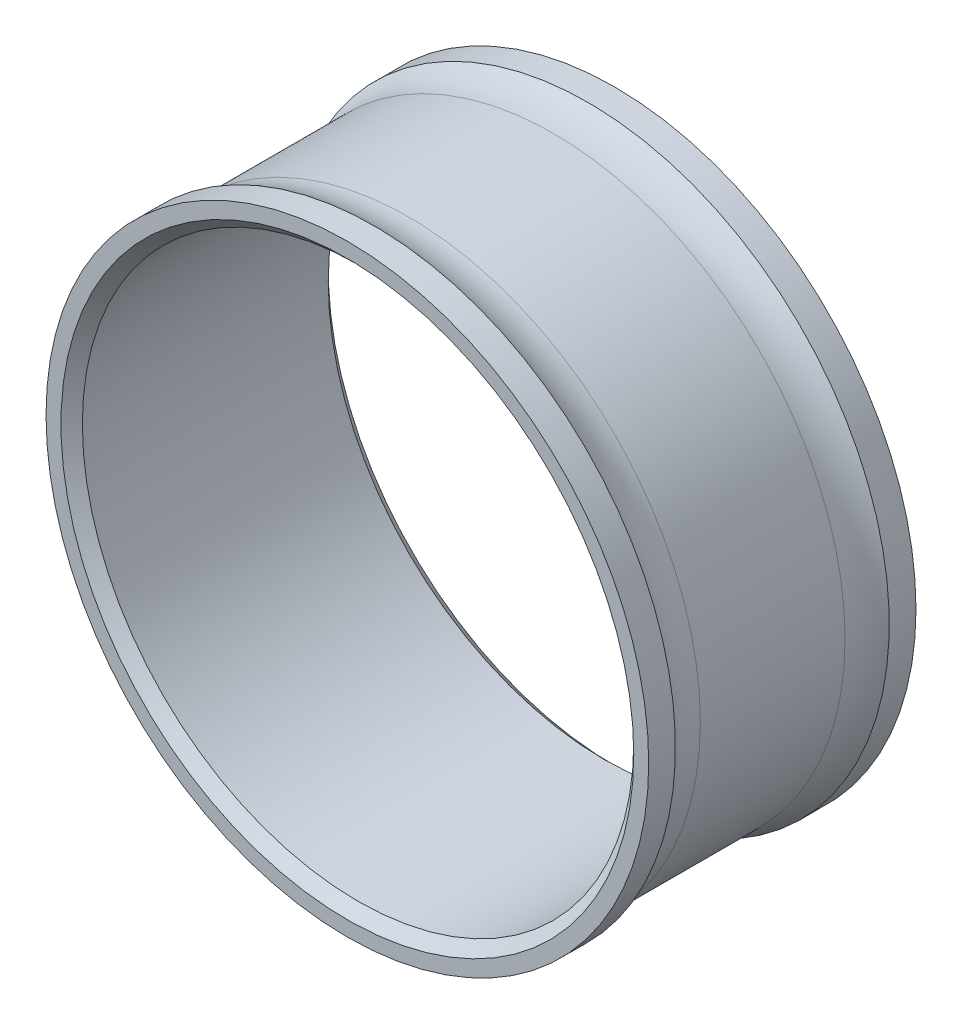
SolidWorks part; units mm, degrees
material "6061-T6 (SS)"
ref_plane "Front Plane" through (0, 0, 0) normal (0, 0, 1) x (1, 0, 0)
ref_plane "Top Plane" through (0, 0, 0) normal (0, 1, 0) x (1, 0, 0)
ref_plane "Right Plane" through (0, 0, 0) normal (1, 0, 0) x (0, 0, -1)
sketch "Sketch1" plane through (0, 0, 0) normal (0, 0, 1) x (1, 0, 0)
  circle A0 centre (0, 0) radius 32.5 construction
  circle A1 centre (0, 0) radius 35.8013
  circle A2 centre (0, 0) radius 32.754
  dimension "D1" = 65
  dimension "D2" = 71.6026
  dimension "D3" = 0.254
extrude "Boss-Extrude1" add sketch "Sketch1" along normal mid plane 31.75
chamfer "Chamfer1" distance 1.27 angle 45 2 edges at (32.754, 0, -15.875) (32.754, 0, 15.875)
sketch "Sketch6" plane through (0, 0, 0) normal (0, 1, 0) x (1, 0, 0)
  line L0 (34.659, -8.5977) -> (34.659, 8.5977)
  line L2 (0, 0) -> (34.659, 0) construction
  line L3 (35.8013, 15.875) -> (-35.8013, 15.875) construction
  line L4 (35.8013, 12.7) -> (35.8013, -12.7)
  line L5 (0, 15.875) -> (0, -15.875) construction
  line L7 (32.754, 14.605) -> (32.754, -15.875) construction
  line L8 (-35.8013, -15.875) -> (35.8013, -15.875) construction
  line L9 (32.754, 14.605) -> (-32.754, 14.605) construction
  line L10 (34.024, 15.875) -> (-34.024, 15.875) construction
  arc A0 (35.8013, 12.7) -> (34.659, 8.5977) centre (42.5965, 8.5977) ccw
  arc A1 (35.8013, -12.7) -> (34.659, -8.5977) centre (42.5965, -8.5977) cw
  point P4 (32.754, 14.605)
  point P9 (35.8013, 15.875)
  point P18 (35.8013, 0)
  dimension "D2" = 7.9375
  dimension "D1" = 1.905
  dimension "D3" = 3.175
revolve "Cut-Revolve2" cut sketch "Sketch6" angle 360 about L5
sketch "Sketch3" plane through (0, 0, 0) normal (0, 1, 0) x (1, 0, 0)
  line L0 (0, 9.525) -> (0, -9.525) construction
  line L1 (3.175, 9.525) -> (3.175, -9.525)
  line L2 (-3.175, 9.525) -> (-3.175, -9.525)
  line L3 (35.8013, 15.875) -> (-35.8013, 15.875) construction
  arc A0 (3.175, 9.525) -> (-3.175, 9.525) centre (0, 9.525) ccw
  arc A1 (-3.175, -9.525) -> (3.175, -9.525) centre (0, -9.525) ccw
  point P3 (0, 0)
  point P8 (0, 12.7)
  dimension "D2" = 3.175
  dimension "D1" = 3.175
extrude "Cut-Extrude1" [suppressed] cut sketch "Sketch3" against normal through all
pattern_circular "CirPattern1" [suppressed] count 19 over 360
sketch "Sketch7" plane through (0, 0, -15.875) normal (0, 0, -1) x (-1, 0, 0)
  circle A0 centre (0, 0) radius 31.75
  circle A1 centre (0, 0) radius 38.1
  dimension "D1" = 63.5
  dimension "D2" = 76.2
sketch "Sketch8" [suppressed] plane through (0, 0, 0) normal (0, 1, 0) x (1, 0, 0)
  line L0 (-2.4644, 9.1974) -> (2.4644, -9.1974) construction
  line L1 (-34.7479, 9.1974) -> (34.7479, 9.1974) construction
  line L2 (-34.7479, -9.1974) -> (34.7479, -9.1974) construction
  line L3 (-5.5312, 8.3756) -> (-0.6024, -10.0191)
  line L4 (0.6024, 10.0191) -> (5.5312, -8.3756)
  line L5 (0, 9.525) -> (0, -9.525) construction
  arc A0 (0.6024, 10.0191) -> (-5.5312, 8.3756) centre (-2.4644, 9.1974) ccw
  arc A1 (-0.6024, -10.0191) -> (5.5312, -8.3756) centre (2.4644, -9.1974) ccw
  arc A2 (3.175, 9.525) -> (-3.175, 9.525) centre (0, 9.525) ccw construction
  dimension "D1" = 15
extrude "Cut-Extrude2" [suppressed] cut sketch "Sketch8" against normal through all
pattern_circular "CirPattern2" [suppressed] count 18 over 360
